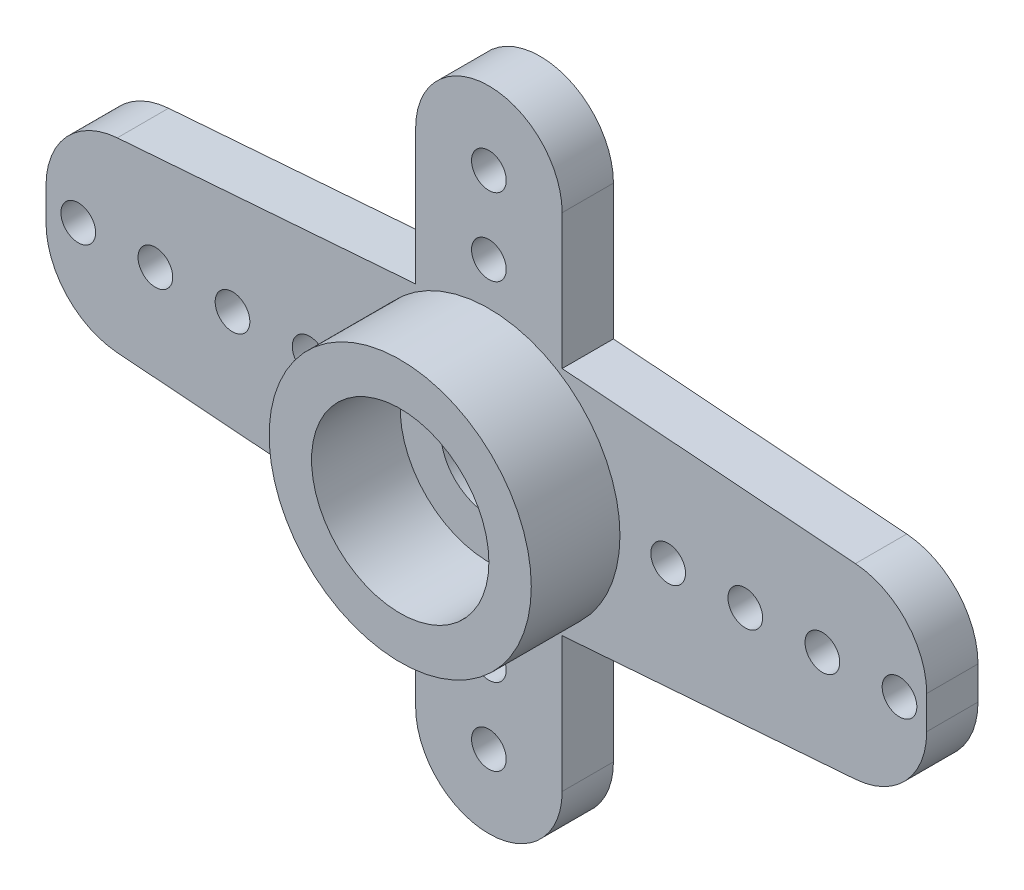
SolidWorks part; units mm, degrees
ref_plane "Ebene vorne" through (0, 0, 0) normal (0, 0, 1) x (1, 0, 0)
ref_plane "Ebene oben" through (0, 0, 0) normal (0, 1, 0) x (1, 0, 0)
ref_plane "Ebene rechts" through (0, 0, 0) normal (1, 0, 0) x (0, 0, -1)
sketch "Skizze1" plane through (0, 0, 0) normal (0, 0, 1) x (1, 0, 0)
  line L0 (0, 3) -> (0, 0) construction
  line L1 (16.65, 0) -> (-16.65, 0) construction
  line L2 (-16.7919, 1.8696) -> (-1.9, 3)
  line L4 (-16.7919, -1.8696) -> (-1.9, -3)
  line L5 (16.7919, -1.8696) -> (1.9, -3)
  line L6 (16.7919, 1.8696) -> (1.9, 3)
  line L7 (-1.9, 3) -> (-1.9, 6.5)
  line L8 (1.9, 3) -> (1.9, 6.5)
  line L9 (1.9, -3) -> (1.9, -6.5)
  line L10 (-1.9, -3) -> (-1.9, -6.5)
  arc A0 (-16.7919, 1.8696) -> (-16.7919, -1.8696) centre (-16.65, 0) ccw
  arc A1 (16.7919, 1.8696) -> (16.7919, -1.8696) centre (16.65, 0) cw
  arc A2 (1.9, 6.5) -> (-1.9, 6.5) centre (0, 6.5) ccw
  arc A3 (1.9, -6.5) -> (-1.9, -6.5) centre (0, -6.5) cw
  dimension "D1" = 3.75
  dimension "D5" = 13
  dimension "D6" = 1.9
  dimension "D2" = 33.3
  dimension "D3" = 6
  dimension "D4" = 3.8
extrude "Aufsatz-Linear austragen1" add sketch "Skizze1" along normal blind 1.33
sketch "Skizze2" plane through (0, 0, 1.33) normal (0, 0, 1) x (1, 0, 0)
  circle A0 centre (0, 0) radius 3.4
  circle A1 centre (0, 0) radius 2.3
  dimension "D1" = 6.8
  dimension "D2" = 4.6
extrude "Aufsatz-Linear austragen2" add sketch "Skizze2" along normal blind 2.3 and the other way up to surface (1.33 mm away) other way up to face at (0, 0, 0)
sketch "Skizze3" plane through (0, 0, 1.33) normal (0, 0, 1) x (1, 0, 0)
  circle A0 centre (0, 0) radius 1.25
  dimension "D1" = 2.5
extrude "Schnitt-Linear austragen1" cut sketch "Skizze3" against normal through all
sketch "Skizze4" plane through (0, 0, 0) normal (0, 0, -1) x (-1, 0, 0)
  circle A0 centre (0, 0) radius 2.35
  dimension "D1" = 4.7
extrude "Schnitt-Linear austragen2" cut sketch "Skizze4" against normal blind 1.1
sketch "Skizze5" plane through (0, 0, 1.33) normal (0, 0, 1) x (1, 0, 0)
  line L0 (0, 6.5) -> (0, 0) construction
  line L1 (0, 0) -> (-16.65, 0) construction
  line L2 (0, 4.5) -> (0, -2) construction
  circle A0 centre (0, 6.5) radius 0.45
  circle A1 centre (-16.65, 0) radius 0.45
  circle A2 centre (0, 4.5) radius 0.45
  circle A3 centre (-14.65, 0) radius 0.45
  circle A4 centre (-12.65, 0) radius 0.45
  circle A5 centre (-10.65, 0) radius 0.45
  circle A6 centre (-8.65, 0) radius 0.45
  circle A7 centre (-6.65, 0) radius 0.45
  circle A8 centre (-4.65, 0) radius 0.45
  circle A9 centre (0, -4.5) radius 0.45
  circle A10 centre (0, -6.5) radius 0.45
  circle A11 centre (4.65, 0) radius 0.45
  circle A12 centre (6.65, 0) radius 0.45
  circle A13 centre (8.65, 0) radius 0.45
  circle A14 centre (10.65, 0) radius 0.45
  circle A15 centre (12.65, 0) radius 0.45
  circle A16 centre (14.65, 0) radius 0.45
  circle A17 centre (16.65, 0) radius 0.45
  dimension "D1" = 0.9
  dimension "D2" = 2
  dimension "D3" = 7
extrude "Schnitt-Linear austragen3" cut sketch "Skizze5" against normal through all
sketch "Skizze7" plane through (0, 0, 0) normal (0, 0, -1) x (-1, 0, 0)
  line L1 (-11.356, -3.7351) -> (-20.1995, -3.7351)
  line L2 (-11.356, -3.7351) -> (-11.356, 4.204)
  line L3 (-11.356, 4.204) -> (-20.1995, 4.204)
  line L4 (-20.1995, -3.7351) -> (-20.1995, 4.204)
  line L5 (11.4871, -3.1686) -> (20.0301, -3.1686)
  line L6 (11.4871, -3.1686) -> (11.4871, 3.4487)
  line L7 (11.4871, 3.4487) -> (20.0301, 3.4487)
  line L8 (20.0301, -3.1686) -> (20.0301, 3.4487)
extrude "Schnitt-Linear austragen4" cut sketch "Skizze7" against normal up to surface (1.33 mm away) up to face at (0.45, 6.5, 1.33)
fillet "Verrundung1" radius 2 4 edges at (-11.4871, -2.2723, 0.665) (-11.4871, 2.2723, 0.665) (11.356, -2.2822, 0.665) (11.356, 2.2822, 0.665)
